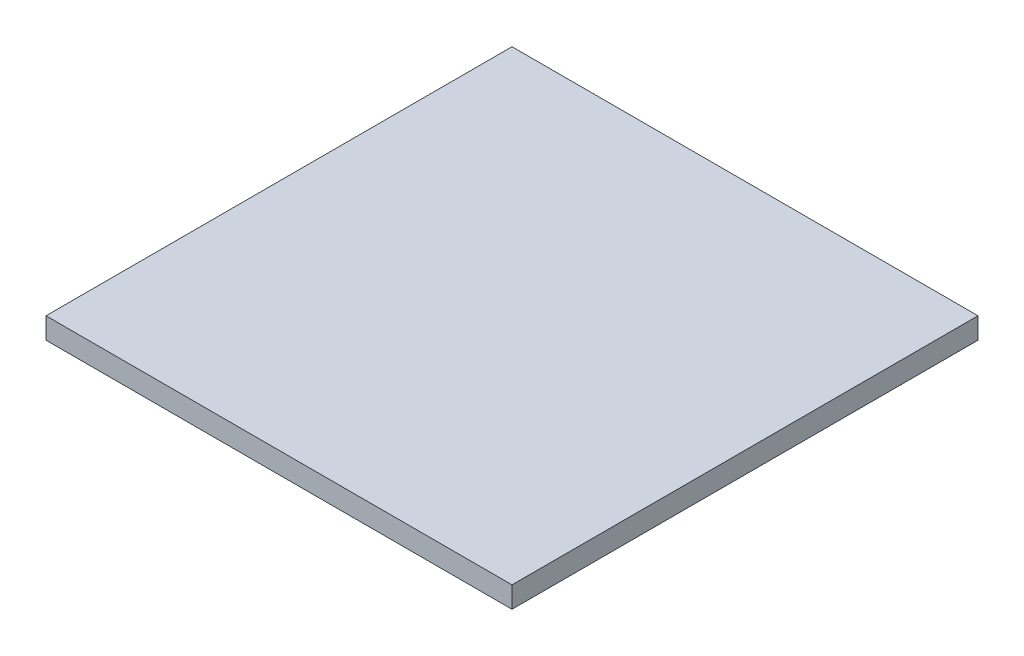
SolidWorks part; units mm, degrees
material "MDF"
ref_plane "Front Plane" through (0, 0, 0) normal (0, 0, 1) x (1, 0, 0)
ref_plane "Top Plane" through (0, 0, 0) normal (0, 1, 0) x (1, 0, 0)
ref_plane "Right Plane" through (0, 0, 0) normal (1, 0, 0) x (0, 0, -1)
sketch "Sketch1" plane through (0, 0, 0) normal (0, 1, 0) x (1, 0, 0)
  line L1 (0, 0) -> (279.4, 0)
  line L2 (0, 0) -> (0, 279.4)
  line L3 (0, 279.4) -> (279.4, 279.4)
  line L4 (279.4, 0) -> (279.4, 279.4)
  dimension "D1" = 279.4
  dimension "D2" = 279.4
extrude "Boss-Extrude1" add sketch "Sketch1" along normal blind 12.7
